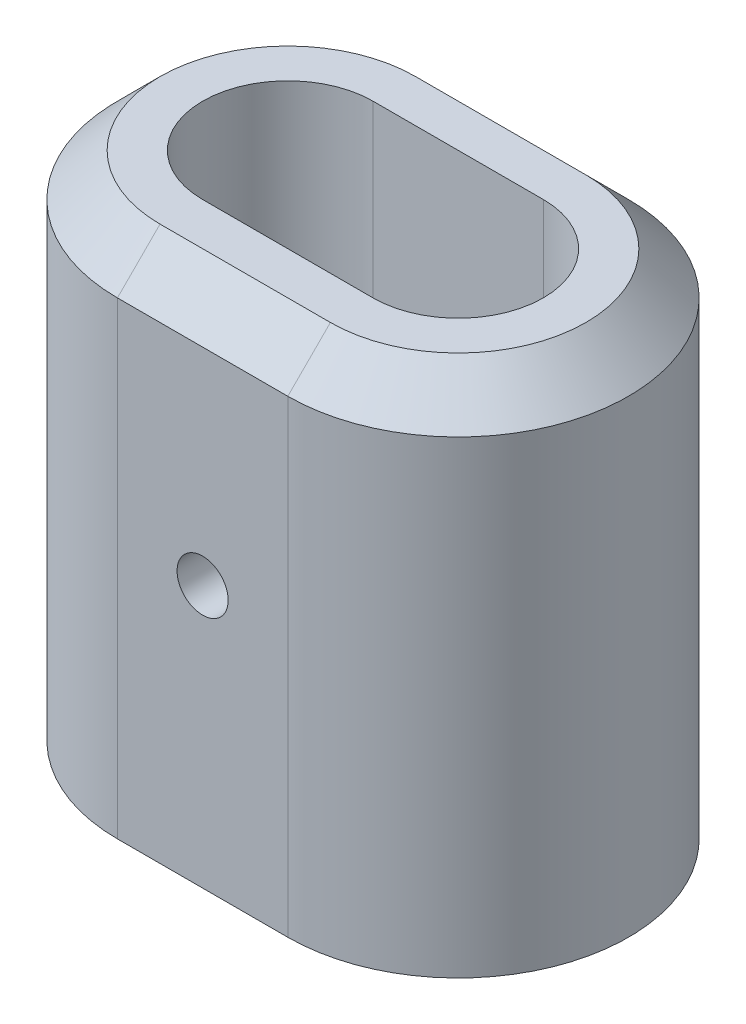
SolidWorks part; units mm, degrees
ref_plane "Front Plane" through (0, 0, 0) normal (0, 0, 1) x (1, 0, 0)
ref_plane "Top Plane" through (0, 0, 0) normal (0, 1, 0) x (1, 0, 0)
ref_plane "Right Plane" through (0, 0, 0) normal (1, 0, 0) x (0, 0, -1)
sketch "Sketch1" plane through (0, 0, 0) normal (0, 1, 0) x (1, 0, 0)
  line L0 (-60, 10) -> (-40, 10)
  line L1 (-60, 20) -> (-40, 20)
  line L2 (-60, -20) -> (-40, -20)
  line L3 (-60, -10) -> (-40, -10)
  arc A0 (-60, 20) -> (-60, -20) centre (-60, 0) ccw
  arc A1 (-40, -20) -> (-40, 20) centre (-40, 0) ccw
  arc A2 (-40, -10) -> (-40, 10) centre (-40, 0) ccw
  arc A3 (-60, 10) -> (-60, -10) centre (-60, 0) ccw
  point P4 (0, 0)
  dimension "D1" = 10
  dimension "D2" = 20
  dimension "D3" = 10
  dimension "D4" = 20
extrude "Boss-Extrude1" add sketch "Sketch1" along normal mid plane 60
chamfer "Chamfer1" distance 5 angle 45 4 edges at (-80, 30, 0) (-50, 30, -20) (-50, 30, 20) (-20, 30, 0)
sketch "Sketch2" plane through (0, 0, 20) normal (0, 0, 1) x (1, 0, 0)
  circle A0 centre (-50, 0.75) radius 3
extrude "Cut-Extrude1" cut sketch "Sketch2" against normal through all
